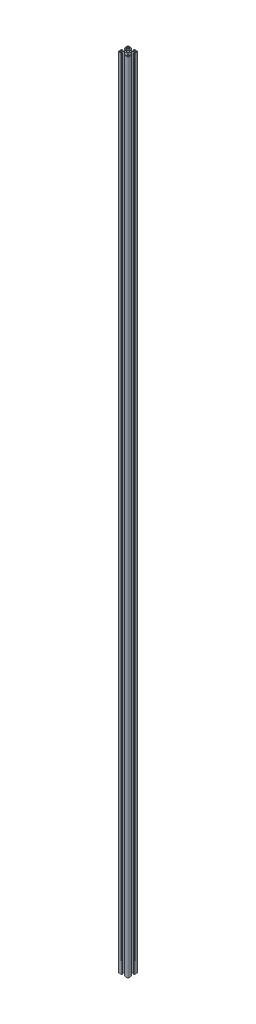
SolidWorks part; units mm, degrees
material "6063-T5"
ref_plane "前视基准面" through (0, 0, 0) normal (0, 0, 1) x (1, 0, 0)
ref_plane "上视基准面" through (0, 0, 0) normal (0, 1, 0) x (1, 0, 0)
ref_plane "右视基准面" through (0, 0, 0) normal (1, 0, 0) x (0, 0, -1)
sketch "草图3" plane through (0, 0, 0) normal (0, 1, 0) x (1, 0, 0)
  line L0 (0, 0) -> (-15, -15) construction
  line L1 (-15, -15) -> (-15, 0) construction
  line L2 (-15, 0) -> (0, 0) construction
  line L3 (-15, -12.5) -> (-15, -5.4)
  line L4 (-14.8, -5.2) -> (-14.4, -5.2)
  line L5 (-14.2, -5) -> (-14.2, -4.3)
  line L6 (-14, -4.1) -> (-13.2, -4.1)
  line L7 (-13.2, -4.1) -> (-13.2, -8.25)
  line L8 (-13.2, -8.25) -> (-9.5228, -8.25)
  line L9 (-9.5228, -8.25) -> (-5.8, -4.5272)
  line L10 (-5.8, -4.5272) -> (-5.8, 4.5272)
  line L11 (-13.2, -12.2) -> (-13.2, -11.05)
  line L12 (-12.2, -10.05) -> (-11.05, -10.05)
  line L13 (-4.5272, -5.8) -> (4.5272, -5.8)
  line L14 (-8.25, -9.5228) -> (-4.5272, -5.8)
  line L15 (-12.2, -13.2) -> (-11.05, -13.2)
  line L16 (-10.05, -12.2) -> (-10.05, -11.05)
  line L17 (-5.2, -14.8) -> (-5.2, -14.4)
  line L18 (-5, -14.2) -> (-4.3, -14.2)
  line L19 (-4.1, -14) -> (-4.1, -13.2)
  line L20 (-4.1, -13.2) -> (-8.25, -13.2)
  line L21 (-8.25, -13.2) -> (-8.25, -9.5228)
  line L22 (-12.5, -15) -> (-5.4, -15)
  line L23 (-12.5, 15) -> (-5.4, 15)
  line L24 (-8.25, 13.2) -> (-8.25, 9.5228)
  line L25 (-4.1, 13.2) -> (-8.25, 13.2)
  line L26 (-4.1, 14) -> (-4.1, 13.2)
  line L27 (-5, 14.2) -> (-4.3, 14.2)
  line L28 (-5.2, 14.8) -> (-5.2, 14.4)
  line L29 (-10.05, 12.2) -> (-10.05, 11.05)
  line L30 (-12.2, 13.2) -> (-11.05, 13.2)
  line L31 (-8.25, 9.5228) -> (-4.5272, 5.8)
  line L32 (-4.5272, 5.8) -> (4.5272, 5.8)
  line L33 (-12.2, 10.05) -> (-11.05, 10.05)
  line L34 (-13.2, 12.2) -> (-13.2, 11.05)
  line L35 (-9.5228, 8.25) -> (-5.8, 4.5272)
  line L36 (-13.2, 8.25) -> (-9.5228, 8.25)
  line L37 (-13.2, 4.1) -> (-13.2, 8.25)
  line L38 (-14, 4.1) -> (-13.2, 4.1)
  line L39 (-14.2, 5) -> (-14.2, 4.3)
  line L40 (-14.8, 5.2) -> (-14.4, 5.2)
  line L41 (-15, 12.5) -> (-15, 5.4)
  line L42 (0, 0) -> (0, -12.3268) construction
  line L43 (15, 12.5) -> (15, 5.4)
  line L44 (14.8, 5.2) -> (14.4, 5.2)
  line L45 (14.2, 5) -> (14.2, 4.3)
  line L46 (14, 4.1) -> (13.2, 4.1)
  line L47 (13.2, 4.1) -> (13.2, 8.25)
  line L48 (13.2, 8.25) -> (9.5228, 8.25)
  line L49 (9.5228, 8.25) -> (5.8, 4.5272)
  line L50 (13.2, 12.2) -> (13.2, 11.05)
  line L51 (12.2, 10.05) -> (11.05, 10.05)
  line L52 (8.25, 9.5228) -> (4.5272, 5.8)
  line L53 (12.2, 13.2) -> (11.05, 13.2)
  line L54 (10.05, 12.2) -> (10.05, 11.05)
  line L55 (5.2, 14.8) -> (5.2, 14.4)
  line L56 (5, 14.2) -> (4.3, 14.2)
  line L57 (4.1, 14) -> (4.1, 13.2)
  line L58 (4.1, 13.2) -> (8.25, 13.2)
  line L59 (8.25, 13.2) -> (8.25, 9.5228)
  line L60 (12.5, 15) -> (5.4, 15)
  line L61 (12.5, -15) -> (5.4, -15)
  line L62 (8.25, -13.2) -> (8.25, -9.5228)
  line L63 (4.1, -13.2) -> (8.25, -13.2)
  line L64 (4.1, -14) -> (4.1, -13.2)
  line L65 (5, -14.2) -> (4.3, -14.2)
  line L66 (5.2, -14.8) -> (5.2, -14.4)
  line L67 (10.05, -12.2) -> (10.05, -11.05)
  line L68 (12.2, -13.2) -> (11.05, -13.2)
  line L69 (8.25, -9.5228) -> (4.5272, -5.8)
  line L70 (12.2, -10.05) -> (11.05, -10.05)
  line L71 (13.2, -12.2) -> (13.2, -11.05)
  line L72 (5.8, -4.5272) -> (5.8, 4.5272)
  line L73 (9.5228, -8.25) -> (5.8, -4.5272)
  line L74 (13.2, -8.25) -> (9.5228, -8.25)
  line L75 (13.2, -4.1) -> (13.2, -8.25)
  line L76 (14, -4.1) -> (13.2, -4.1)
  line L77 (14.2, -5) -> (14.2, -4.3)
  line L78 (14.8, -5.2) -> (14.4, -5.2)
  line L79 (15, -12.5) -> (15, -5.4)
  circle A0 centre (0, 0) radius 3.4
  arc A1 (-12.5, 15) -> (-15, 12.5) centre (-12.5, 12.5) ccw
  arc A2 (15, 12.5) -> (12.5, 15) centre (12.5, 12.5) ccw
  arc A3 (12.5, -15) -> (15, -12.5) centre (12.5, -12.5) ccw
  arc A4 (-15, -12.5) -> (-12.5, -15) centre (-12.5, -12.5) ccw
  arc A5 (-12.2, 13.2) -> (-13.2, 12.2) centre (-12.2, 12.2) ccw
  arc A6 (-12.2, 10.05) -> (-13.2, 11.05) centre (-12.2, 11.05) cw
  arc A7 (-10.05, 11.05) -> (-11.05, 10.05) centre (-11.05, 11.05) cw
  arc A8 (-10.05, 12.2) -> (-11.05, 13.2) centre (-11.05, 12.2) ccw
  arc A9 (11.05, 10.05) -> (10.05, 11.05) centre (11.05, 11.05) cw
  arc A10 (11.05, 13.2) -> (10.05, 12.2) centre (11.05, 12.2) ccw
  arc A11 (13.2, 12.2) -> (12.2, 13.2) centre (12.2, 12.2) ccw
  arc A12 (13.2, 11.05) -> (12.2, 10.05) centre (12.2, 11.05) cw
  arc A13 (12.2, -10.05) -> (13.2, -11.05) centre (12.2, -11.05) cw
  arc A14 (10.05, -11.05) -> (11.05, -10.05) centre (11.05, -11.05) cw
  arc A15 (10.05, -12.2) -> (11.05, -13.2) centre (11.05, -12.2) ccw
  arc A16 (12.2, -13.2) -> (13.2, -12.2) centre (12.2, -12.2) ccw
  arc A17 (-13.2, -11.05) -> (-12.2, -10.05) centre (-12.2, -11.05) cw
  arc A18 (-11.05, -10.05) -> (-10.05, -11.05) centre (-11.05, -11.05) cw
  arc A19 (-11.05, -13.2) -> (-10.05, -12.2) centre (-11.05, -12.2) ccw
  arc A20 (-13.2, -12.2) -> (-12.2, -13.2) centre (-12.2, -12.2) ccw
  arc A21 (-15, -5.4) -> (-14.8, -5.2) centre (-14.8, -5.4) cw
  arc A22 (-14.4, -5.2) -> (-14.2, -5) centre (-14.4, -5) ccw
  arc A23 (-14.2, -4.3) -> (-14, -4.1) centre (-14, -4.3) cw
  arc A24 (-14, 4.1) -> (-14.2, 4.3) centre (-14, 4.3) cw
  arc A25 (-14.2, 5) -> (-14.4, 5.2) centre (-14.4, 5) ccw
  arc A26 (-14.8, 5.2) -> (-15, 5.4) centre (-14.8, 5.4) cw
  arc A27 (-5.4, 15) -> (-5.2, 14.8) centre (-5.4, 14.8) cw
  arc A28 (-5, 14.2) -> (-5.2, 14.4) centre (-5, 14.4) cw
  arc A29 (-4.1, 14) -> (-4.3, 14.2) centre (-4.3, 14) ccw
  arc A30 (5.2, 14.8) -> (5.4, 15) centre (5.4, 14.8) cw
  arc A31 (5.2, 14.4) -> (5, 14.2) centre (5, 14.4) cw
  arc A32 (4.3, 14.2) -> (4.1, 14) centre (4.3, 14) ccw
  arc A33 (15, 5.4) -> (14.8, 5.2) centre (14.8, 5.4) cw
  arc A34 (14.4, 5.2) -> (14.2, 5) centre (14.4, 5) ccw
  arc A35 (14.2, 4.3) -> (14, 4.1) centre (14, 4.3) cw
  arc A36 (14, -4.1) -> (14.2, -4.3) centre (14, -4.3) cw
  arc A37 (14.2, -5) -> (14.4, -5.2) centre (14.4, -5) ccw
  arc A38 (14.8, -5.2) -> (15, -5.4) centre (14.8, -5.4) cw
  arc A39 (5.4, -15) -> (5.2, -14.8) centre (5.4, -14.8) cw
  arc A40 (5, -14.2) -> (5.2, -14.4) centre (5, -14.4) cw
  arc A41 (4.1, -14) -> (4.3, -14.2) centre (4.3, -14) ccw
  arc A42 (-5.2, -14.4) -> (-5, -14.2) centre (-5, -14.4) cw
  arc A43 (-4.3, -14.2) -> (-4.1, -14) centre (-4.3, -14) ccw
  arc A44 (-5.2, -14.8) -> (-5.4, -15) centre (-5.4, -14.8) cw
  point P38 (-5.8, 0)
  point P46 (0, 5.8)
  point P47 (0, -5.8)
  point P83 (5.8, 0)
  point P87 (-15, 15)
  point P90 (15, 15)
  point P93 (15, -15)
  point P99 (-13.2, 13.2)
  point P102 (-13.2, 10.05)
  point P105 (-10.05, 10.05)
  point P108 (-10.05, 13.2)
  point P111 (10.05, 10.05)
  point P114 (10.05, 13.2)
  point P117 (13.2, 13.2)
  point P120 (13.2, 10.05)
  point P123 (13.2, -10.05)
  point P126 (10.05, -10.05)
  point P129 (10.05, -13.2)
  point P132 (13.2, -13.2)
  point P135 (-13.2, -10.05)
  point P138 (-10.05, -10.05)
  point P141 (-10.05, -13.2)
  point P144 (-13.2, -13.2)
  point P147 (-15, -5.2)
  point P150 (-14.2, -5.2)
  point P153 (-14.2, -4.1)
  point P156 (-14.2, 4.1)
  point P159 (-14.2, 5.2)
  point P162 (-15, 5.2)
  point P165 (-5.2, 15)
  point P168 (-5.2, 14.2)
  point P171 (-4.1, 14.2)
  point P174 (5.2, 15)
  point P177 (5.2, 14.2)
  point P180 (4.1, 14.2)
  point P183 (15, 5.2)
  point P186 (14.2, 5.2)
  point P189 (14.2, 4.1)
  point P192 (14.2, -4.1)
  point P195 (14.2, -5.2)
  point P198 (15, -5.2)
  point P201 (5.2, -15)
  point P204 (5.2, -14.2)
  point P207 (4.1, -14.2)
  point P210 (-5.2, -14.2)
  point P213 (-4.1, -14.2)
  point P216 (-5.2, -15)
  dimension "D11" = 6.8
  dimension "D12" = 2.5
  dimension "D13" = 1
  dimension "D14" = 0.2
  dimension "D2" = 15
  dimension "D3" = 4.1
  dimension "D4" = 5.2
  dimension "D5" = 0.8
  dimension "D6" = 1.8
  dimension "D7" = 9.2
  dimension "D8" = 8.25
  dimension "D9" = 0.9
  dimension "D10" = 1.8
extrude "凸台-拉伸1" add sketch "草图3" along normal blind 2400
